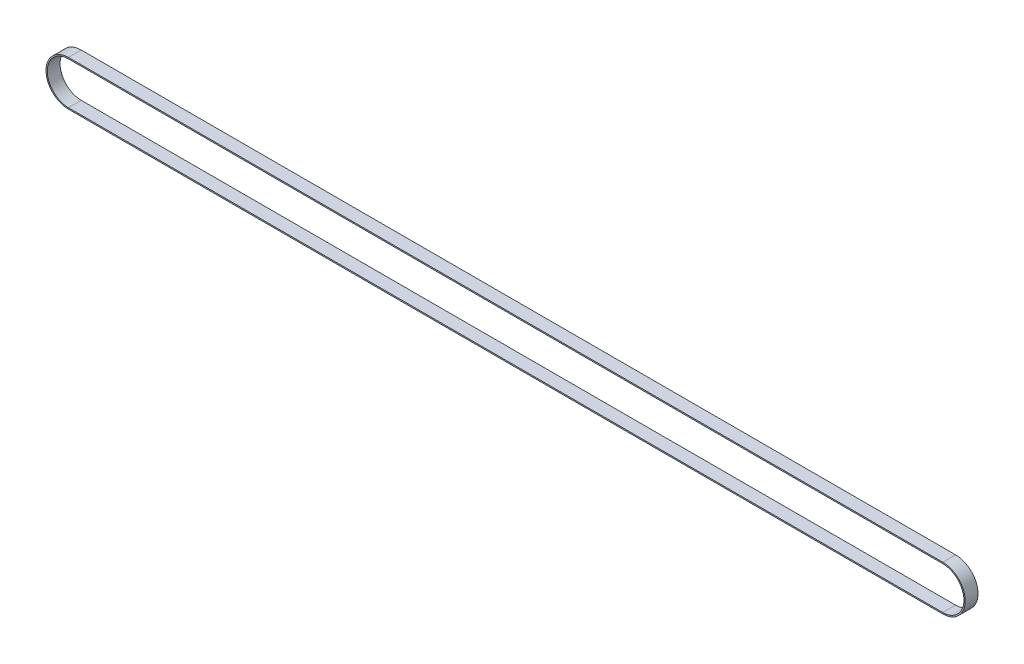
SolidWorks part; units mm, degrees
ref_plane "Front Plane" through (0, 0, 0) normal (0, 0, 1) x (1, 0, 0)
ref_plane "Top Plane" through (0, 0, 0) normal (0, 1, 0) x (1, 0, 0)
ref_plane "Right Plane" through (0, 0, 0) normal (1, 0, 0) x (0, 0, -1)
sketch "Sketch1" plane through (0, 0, 0) normal (0, 0, 1) x (1, 0, 0)
  line L0 (0, 0) -> (1365, 0) construction
  line L1 (0, 35) -> (1365, 35)
  line L2 (0, -35) -> (1365, -35)
  arc A0 (0, 35) -> (0, -35) centre (0, 0) ccw
  arc A1 (1365, -35) -> (1365, 35) centre (1365, 0) ccw
  point P3 (682.5, 0)
extrude "Boss-Extrude2" add sketch "Sketch1" along normal blind 20
sketch "Sketch3" plane through (0, 0, 20) normal (0, 0, 1) x (1, 0, 0)
  line L0 (0, 0) -> (1365, 0) construction
  line L1 (0, 33) -> (1365, 33)
  line L2 (0, -33) -> (1365, -33)
  arc A0 (0, 33) -> (0, -33) centre (0, 0) ccw
  arc A1 (1365, -33) -> (1365, 33) centre (1365, 0) ccw
  point P3 (682.5, 0)
extrude "Cut-Extrude3" cut sketch "Sketch3" against normal blind 20
